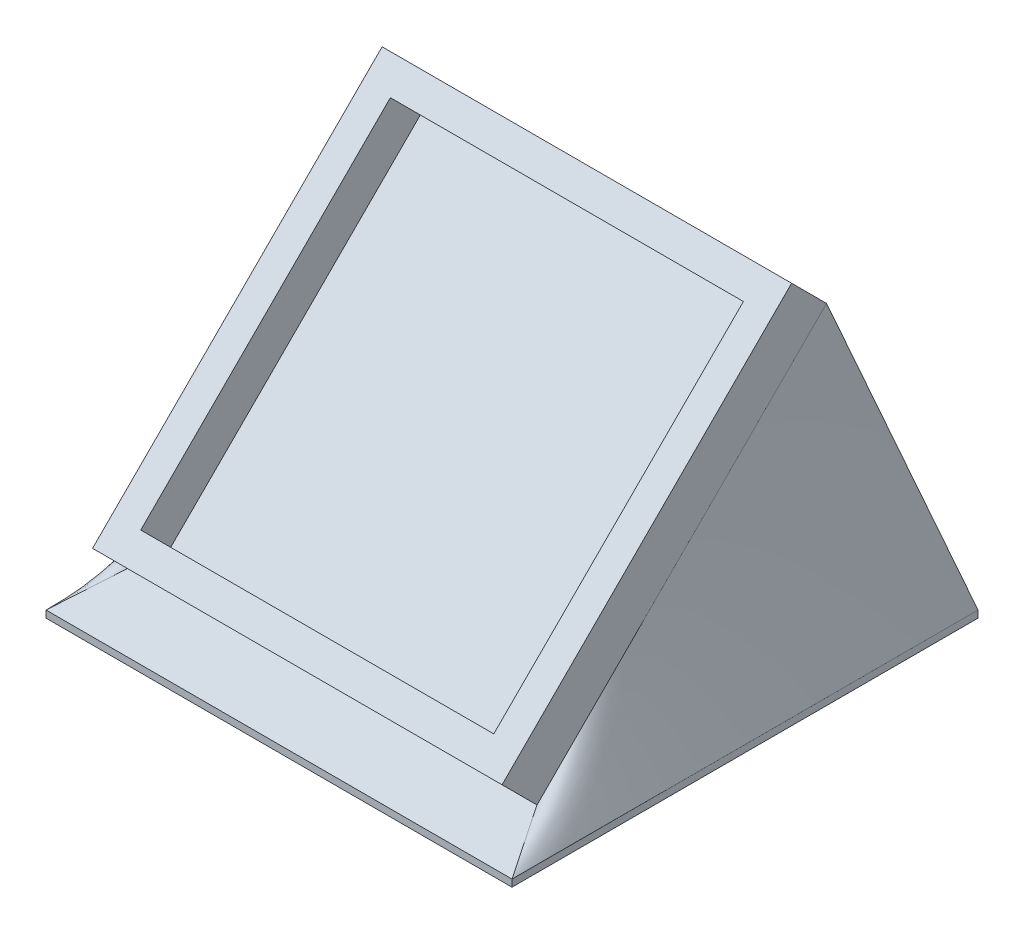
SolidWorks part; units mm, degrees
ref_plane "Front Plane" through (0, 0, 0) normal (0, 0, 1) x (1, 0, 0)
ref_plane "Top Plane" through (0, 0, 0) normal (0, 1, 0) x (1, 0, 0)
ref_plane "Right Plane" through (0, 0, 0) normal (1, 0, 0) x (0, 0, -1)
sketch "Sketch1" plane through (0, 0, 0) normal (0, 1, 0) x (1, 0, 0)
  line L1 (-22.2888, 13.0013) -> (14.5412, 13.0013)
  line L2 (-22.2888, 13.0013) -> (-22.2888, -23.8287)
  line L3 (-22.2888, -23.8287) -> (14.5412, -23.8287)
  line L4 (14.5412, 13.0013) -> (14.5412, -23.8287)
  dimension "D1" = 36.83
  dimension "D2" = 36.83
extrude "Boss-Extrude1" add sketch "Sketch1" along normal blind 0.635
sketch "Sketch2" plane through (0, 0.635, 0) normal (0, 1, 0) x (1, 0, 0)
  line L0 (14.5412, 13.0013) -> (-22.2888, 13.0013) construction
  line L1 (-19.7488, 10.4613) -> (12.0012, 10.4613)
  line L2 (-19.7488, 10.4613) -> (-19.7488, -21.2887)
  line L3 (-19.7488, -21.2887) -> (12.0012, -21.2887)
  line L4 (12.0012, 10.4613) -> (12.0012, -21.2887)
  line L5 (-22.2888, 13.0013) -> (-22.2888, -23.8287) construction
  line L7 (-22.2888, 13.0013) -> (14.5412, 13.0013)
  line L8 (-22.2888, 13.0013) -> (-22.2888, -23.8287)
  line L9 (-22.2888, -23.8287) -> (14.5412, -23.8287)
  line L10 (14.5412, 13.0013) -> (14.5412, -23.8287)
  dimension "D1" = 31.75
  dimension "D2" = 31.75
  dimension "D3" = 2.54
  dimension "D4" = 2.54
extrude "Boss-Extrude2" add sketch "Sketch2" along normal blind 3.81 contours L8 L7 L10 L9 | L2 L1 L4 L3
move or copy body "Body-Move/Copy1" bodies to move or copy 102 copy no translate (0, 20.32, 0)
sketch "Sketch3" plane through (0, 0, 0) normal (0, 1, 0) x (1, 0, 0)
  line L0 (-22.2888, 13.0013) -> (-22.2888, -23.8287) construction
  line L1 (-24.8288, 15.5413) -> (17.0812, 15.5413)
  line L2 (-24.8288, 15.5413) -> (-24.8288, -26.3687)
  line L3 (-24.8288, -26.3687) -> (17.0812, -26.3687)
  line L4 (17.0812, 15.5413) -> (17.0812, -26.3687)
  line L5 (-22.2888, -23.8287) -> (14.5412, -23.8287) construction
  dimension "D1" = 41.91
  dimension "D2" = 41.91
  dimension "D3" = 2.54
  dimension "D4" = 2.54
extrude "Boss-Extrude3" add sketch "Sketch3" along normal blind 0.635 separate body
move or copy body "Body-Move/Copy2" bodies to move or copy 103 copy no rotation origin (0, 4.7625, 5.4137) rotation axis (1, 0, 0) rotation angle 45
move or copy body "Body-Move/Copy3" bodies to move or copy 105 copy no translate (0, 0, -7.8554)
loft "Loft1" add section face at (-3.8738, 15.7633, 8.5591) section face at (-3.8738, 0.635, 5.4137)
sketch "Sketch4" plane through (0, 16.6235, -16.6235) normal (0, 0.7071, -0.7071) x (1, 0, 0)
  text T0 "45 x 0"
extrude "Cut-Extrude1" cut sketch "Sketch4" against normal blind 0.635
